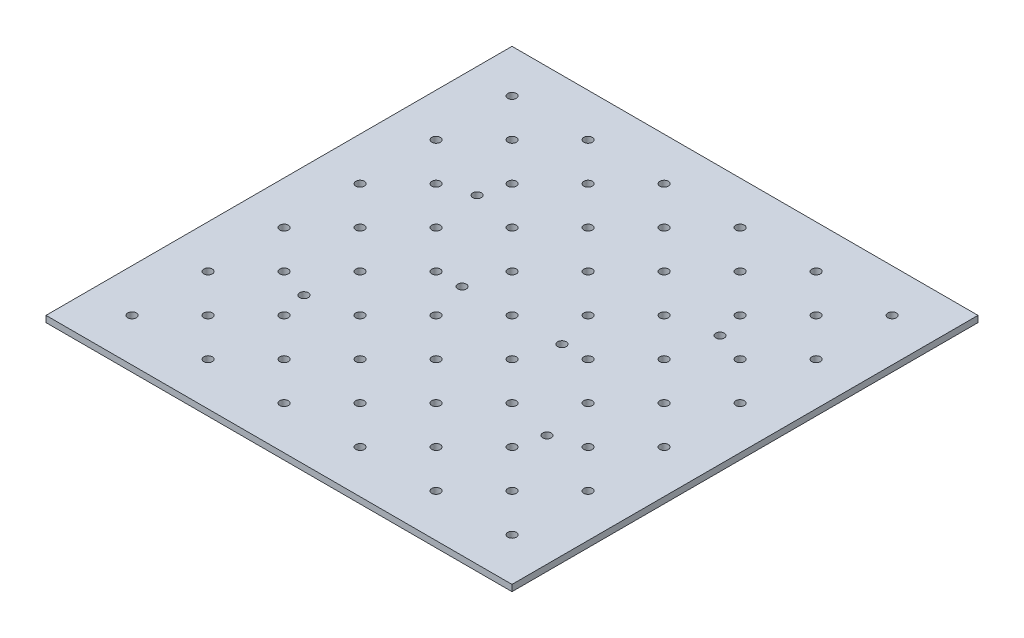
SolidWorks part; units mm, degrees
ref_plane "Front Plane" through (0, 0, 0) normal (0, 0, 1) x (1, 0, 0)
ref_plane "Top Plane" through (0, 0, 0) normal (0, 1, 0) x (1, 0, 0)
ref_plane "Right Plane" through (0, 0, 0) normal (1, 0, 0) x (0, 0, -1)
sketch "Sketch1" plane through (0, 0, 0) normal (0, 1, 0) x (1, 0, 0)
  line L1 (-177.8, -177.8) -> (177.8, -177.8)
  line L2 (-177.8, -177.8) -> (-177.8, 177.8)
  line L3 (-177.8, 177.8) -> (177.8, 177.8)
  line L4 (177.8, -177.8) -> (177.8, 177.8)
  line L5 (-177.8, -177.8) -> (177.8, 177.8) construction
  line L6 (-177.8, 177.8) -> (177.8, -177.8) construction
  point P0 (0, 0)
  dimension "D1" = 355.6
  dimension "D2" = 355.6
extrude "Boss-Extrude1" add sketch "Sketch1" along normal blind 4.826 contours L4 L3 L2 L1
sketch "Sketch3" plane through (0, 0, 0) normal (0, -1, 0) x (1, 0, 0)
  circle A0 centre (92.71, -66.04) radius 3.2639
  circle A1 centre (92.71, 66.04) radius 3.2639
  circle A2 centre (38.1, 0) radius 3.2639
  circle A3 centre (-38.1, 0) radius 3.2639
  circle A4 centre (-92.71, 66.04) radius 3.2639
  circle A5 centre (-92.71, -66.04) radius 3.2639
extrude "Cut-Extrude2" cut sketch "Sketch3" against normal through all
sketch "Sketch5" plane through (0, 0, 0) normal (0, -1, 0) x (1, 0, 0)
  line L0 (177.8, 177.8) -> (177.8, -177.8) construction
  line L1 (-177.8, -177.8) -> (177.8, -177.8) construction
  circle A0 centre (145.034, -145.034) radius 3.2639
  circle A1 centre (87.034, -145.034) radius 3.2639
  circle A2 centre (29.034, -145.034) radius 3.2639
  circle A3 centre (-28.966, -145.034) radius 3.2639
  circle A4 centre (-86.966, -145.034) radius 3.2639
  circle A5 centre (-144.966, -145.034) radius 3.2639
  circle A6 centre (145.034, -87.034) radius 3.2639
  circle A7 centre (87.034, -87.034) radius 3.2639
  circle A8 centre (29.034, -87.034) radius 3.2639
  circle A9 centre (-28.966, -87.034) radius 3.2639
  circle A10 centre (-86.966, -87.034) radius 3.2639
  circle A11 centre (-144.966, -87.034) radius 3.2639
  circle A12 centre (145.034, -29.034) radius 3.2639
  circle A13 centre (87.034, -29.034) radius 3.2639
  circle A14 centre (29.034, -29.034) radius 3.2639
  circle A15 centre (-28.966, -29.034) radius 3.2639
  circle A16 centre (-86.966, -29.034) radius 3.2639
  circle A17 centre (-144.966, -29.034) radius 3.2639
  circle A18 centre (145.034, 28.966) radius 3.2639
  circle A19 centre (87.034, 28.966) radius 3.2639
  circle A20 centre (29.034, 28.966) radius 3.2639
  circle A21 centre (-28.966, 28.966) radius 3.2639
  circle A22 centre (-86.966, 28.966) radius 3.2639
  circle A23 centre (-144.966, 28.966) radius 3.2639
  circle A24 centre (145.034, 86.966) radius 3.2639
  circle A25 centre (87.034, 86.966) radius 3.2639
  circle A26 centre (29.034, 86.966) radius 3.2639
  circle A27 centre (-28.966, 86.966) radius 3.2639
  circle A28 centre (-86.966, 86.966) radius 3.2639
  circle A29 centre (-144.966, 86.966) radius 3.2639
  circle A30 centre (145.034, 144.966) radius 3.2639
  circle A31 centre (87.034, 144.966) radius 3.2639
  circle A32 centre (29.034, 144.966) radius 3.2639
  circle A33 centre (-28.966, 144.966) radius 3.2639
  circle A34 centre (-86.966, 144.966) radius 3.2639
  circle A35 centre (-144.966, 144.966) radius 3.2639
  dimension "D1" = 6.5278
  dimension "D2" = 32.766
  dimension "D3" = 32.766
  dimension "D4" = 6
  dimension "D5" = 6
extrude "Cut-Extrude3" cut sketch "Sketch5" against normal through all
sketch "Sketch6" plane through (0, 0, 0) normal (0, -1, 0) x (1, 0, 0)
  circle A0 centre (116.034, -116.034) radius 3.2639
  circle A1 centre (145.034, -145.034) radius 3.2639 construction
  circle A2 centre (87.034, -145.034) radius 3.2639 construction
  circle A3 centre (58.034, -116.034) radius 3.2639
  circle A4 centre (0.034, -116.034) radius 3.2639
  circle A5 centre (-57.966, -116.034) radius 3.2639
  circle A6 centre (-115.966, -116.034) radius 3.2639
  circle A7 centre (116.034, -58.034) radius 3.2639
  circle A8 centre (58.034, -58.034) radius 3.2639
  circle A9 centre (0.034, -58.034) radius 3.2639
  circle A10 centre (-57.966, -58.034) radius 3.2639
  circle A11 centre (-115.966, -58.034) radius 3.2639
  circle A12 centre (116.034, -0.034) radius 3.2639
  circle A13 centre (58.034, -0.034) radius 3.2639
  circle A14 centre (0.034, -0.034) radius 3.2639
  circle A15 centre (-57.966, -0.034) radius 3.2639
  circle A16 centre (-115.966, -0.034) radius 3.2639
  circle A17 centre (116.034, 57.966) radius 3.2639
  circle A18 centre (58.034, 57.966) radius 3.2639
  circle A19 centre (0.034, 57.966) radius 3.2639
  circle A20 centre (-57.966, 57.966) radius 3.2639
  circle A21 centre (-115.966, 57.966) radius 3.2639
  circle A22 centre (116.034, 115.966) radius 3.2639
  circle A23 centre (58.034, 115.966) radius 3.2639
  circle A24 centre (0.034, 115.966) radius 3.2639
  circle A25 centre (-57.966, 115.966) radius 3.2639
  circle A26 centre (-115.966, 115.966) radius 3.2639
  dimension "D1" = 29
  dimension "D2" = 6.5278
  dimension "D3" = 29
  dimension "D4" = 5
  dimension "D5" = 5
extrude "Cut-Extrude4" cut sketch "Sketch6" against normal through all
